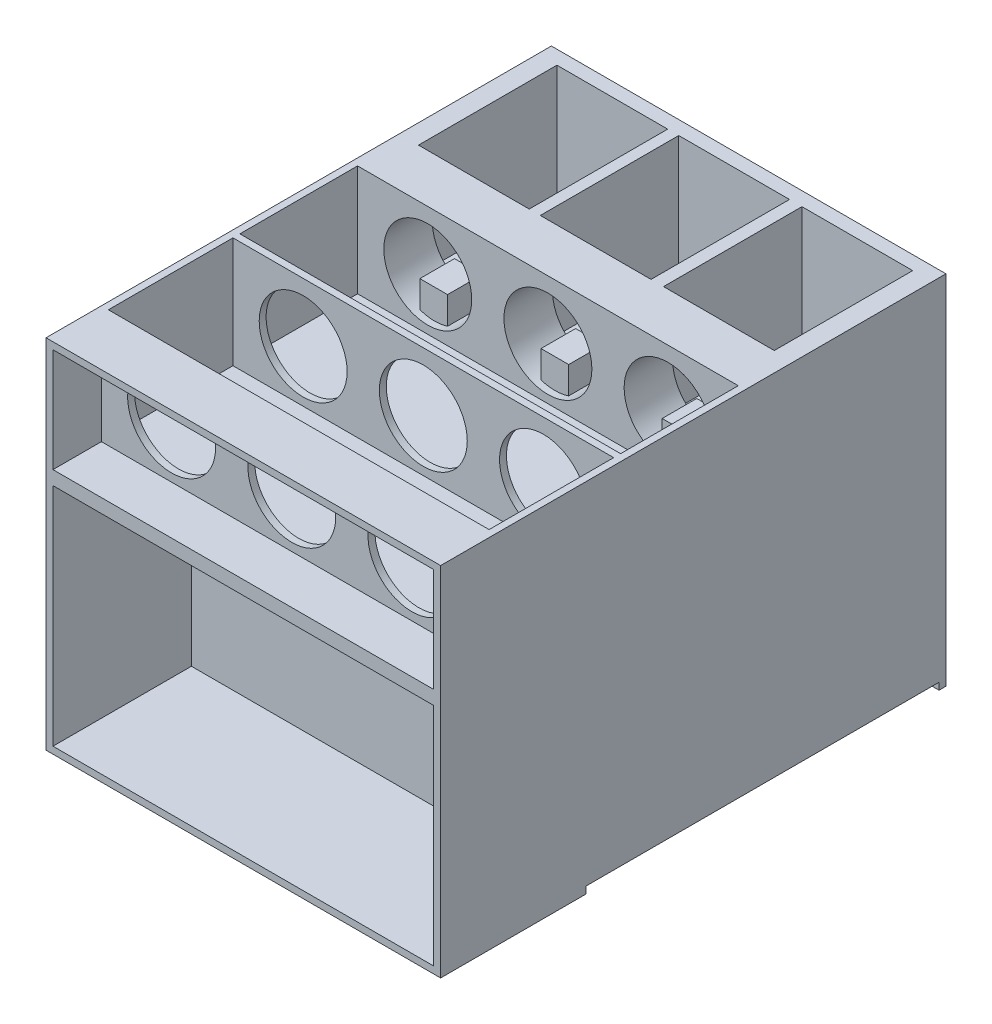
SolidWorks part; units mm, degrees
ref_plane "Front Plane" through (0, 0, 0) normal (0, 0, 1) x (1, 0, 0)
ref_plane "Top Plane" through (0, 0, 0) normal (0, 1, 0) x (1, 0, 0)
ref_plane "Right Plane" through (0, 0, 0) normal (1, 0, 0) x (0, 0, -1)
sketch "Sketch2" plane through (0, 0, 0) normal (0, 0, 1) x (1, 0, 0)
  line L1 (-133.1116, 114.3526) -> (151.8884, 114.3526)
  line L2 (-133.1116, 114.3526) -> (-133.1116, -143.6474)
  line L3 (-133.1116, -143.6474) -> (151.8884, -143.6474)
  line L4 (151.8884, 114.3526) -> (151.8884, -143.6474)
  dimension "D1" = 258
  dimension "D2" = 285
extrude "Boss-Extrude1" add sketch "Sketch2" along normal blind 365
sketch "Sketch3" plane through (0, 0, 365) normal (0, 0, 1) x (1, 0, 0)
  line L0 (151.8884, 114.3526) -> (-133.1116, 114.3526) construction
  line L1 (-128.1116, 109.3526) -> (146.8884, 109.3526)
  line L2 (-128.1116, 109.3526) -> (-128.1116, 34.3526)
  line L3 (-128.1116, 34.3526) -> (146.8884, 34.3526)
  line L4 (146.8884, 109.3526) -> (146.8884, 34.3526)
  line L5 (-133.1116, 114.3526) -> (-133.1116, -143.6474) construction
  line L6 (151.8884, -143.6474) -> (151.8884, 114.3526) construction
  line L7 (-133.1116, -143.6474) -> (151.8884, -143.6474) construction
  line L8 (-128.1116, 24.3526) -> (146.8884, 24.3526)
  line L9 (-128.1116, 24.3526) -> (-128.1116, -138.6474)
  line L10 (-128.1116, -138.6474) -> (146.8884, -138.6474)
  line L11 (146.8884, 24.3526) -> (146.8884, -138.6474)
  dimension "D1" = 5
  dimension "D2" = 5
  dimension "D3" = 5
  dimension "D4" = 75
  dimension "D5" = 10
  dimension "D6" = 5
  dimension "D7" = 5
  dimension "D8" = 5
extrude "Cut-Extrude1" cut sketch "Sketch3" against normal blind 35 contours L2 L1 L4 L3
sketch "Sketch4" plane through (0, 0, 330) normal (0, 0, 1) x (1, 0, 0)
  line L1 (146.8884, 109.3526) -> (146.8884, 34.3526) construction
  line L2 (-128.1116, 109.3526) -> (-128.1116, 34.3526) construction
  line L4 (-128.1116, 109.3526) -> (146.8884, 109.3526) construction
  line L5 (-128.1116, 109.3526) -> (146.8884, 109.3526) construction
  circle A0 centre (-77.4116, 71.8526) radius 31.75
  circle A1 centre (9.3884, 71.8526) radius 31.75
  circle A2 centre (96.1884, 71.8526) radius 31.75
  dimension "D1" = 63.5
  dimension "D2" = 63.5
  dimension "D3" = 63.5
  dimension "D4" = 50.7
  dimension "D5" = 50.7
  dimension "D6" = 137.5
  dimension "D7" = 37.5
  dimension "D8" = 37.5
sketch "Sketch5" plane through (0, 114.3526, 0) normal (0, 1, 0) x (1, 0, 0)
  line L0 (-133.1116, -365) -> (-133.1116, 0) construction
  line L1 (-119.1116, -10) -> (-39.1116, -10)
  line L2 (-119.1116, -10) -> (-119.1116, -110)
  line L3 (-119.1116, -110) -> (-39.1116, -110)
  line L4 (-39.1116, -10) -> (-39.1116, -110)
  line L5 (-31.1116, -10) -> (48.8884, -10)
  line L6 (-31.1116, -10) -> (-31.1116, -110)
  line L7 (-31.1116, -110) -> (48.8884, -110)
  line L8 (48.8884, -10) -> (48.8884, -110)
  line L9 (57.8884, -10) -> (137.8884, -10)
  line L10 (57.8884, -10) -> (57.8884, -110)
  line L11 (57.8884, -110) -> (137.8884, -110)
  line L12 (137.8884, -10) -> (137.8884, -110)
  line L13 (151.8884, 0) -> (-133.1116, 0) construction
  line L14 (151.8884, -365) -> (151.8884, 0) construction
  dimension "D1" = 14
  dimension "D2" = 100
  dimension "D3" = 10
  dimension "D4" = 10
  dimension "D5" = 100
  dimension "D6" = 10
  dimension "D7" = 100
  dimension "D8" = 8
  dimension "8" = 80
  dimension "D9" = 80
  dimension "D10" = 80
  dimension "D11" = 14
  dimension "D12" = 9
  dimension "D13" = 9
  dimension "D14" = 10
extrude "Cut-Extrude2" cut sketch "Sketch5" against normal blind 81 contours L6 L5 L8 L7 | L10 L9 L12 L11 | L2 L1 L4 L3
extrude "Cut-Extrude4" cut sketch "Sketch4" against normal blind 276 contours A0 | A2 | A1
sketch "Sketch6" plane through (0, 114.3526, 0) normal (0, 1, 0) x (1, 0, 0)
  line L0 (151.8884, -365) -> (-133.1116, -365) construction
  line L1 (-128.1116, -145) -> (146.8884, -145)
  line L2 (-128.1116, -145) -> (-128.1116, -230)
  line L3 (-128.1116, -230) -> (146.8884, -230)
  line L4 (146.8884, -145) -> (146.8884, -230)
  line L5 (-128.1116, -235) -> (146.8884, -235)
  line L6 (-128.1116, -235) -> (-128.1116, -325)
  line L7 (-128.1116, -325) -> (146.8884, -325)
  line L8 (146.8884, -235) -> (146.8884, -325)
  line L9 (-133.1116, -365) -> (-133.1116, 0) construction
  line L10 (151.8884, -365) -> (151.8884, 0) construction
  line L11 (-119.1116, -110) -> (-39.1116, -110) construction
  point P14 (-128.1116, -187.5)
  dimension "D1" = 40
  dimension "D2" = 5
  dimension "D3" = 5
  dimension "D4" = 90
  dimension "D5" = 90
  dimension "D6" = 5
  dimension "D7" = 5
  dimension "D8" = 5
  dimension "D9" = 35
extrude "Cut-Extrude6" cut sketch "Sketch6" against normal blind 80
sketch "Sketch8" plane through (0, 0, 365) normal (0, 0, 1) x (1, 0, 0)
  line L0 (-128.1116, 34.3526) -> (146.8884, 34.3526) construction
  line L1 (-128.1116, 24.3526) -> (146.8884, 24.3526)
  line L2 (-128.1116, 24.3526) -> (-128.1116, -138.6474)
  line L3 (-128.1116, -138.6474) -> (146.8884, -138.6474)
  line L4 (146.8884, 24.3526) -> (146.8884, -138.6474)
  line L5 (-133.1116, 114.3526) -> (-133.1116, -143.6474) construction
  line L6 (151.8884, -143.6474) -> (151.8884, 114.3526) construction
  line L7 (-133.1116, -143.6474) -> (151.8884, -143.6474) construction
  dimension "D1" = 10
  dimension "D2" = 5
  dimension "D3" = 5
  dimension "0.5" = 5
extrude "Cut-Extrude10" cut sketch "Sketch8" against normal blind 100
sketch "Sketch16" plane through (0, -143.6474, 0) normal (0, -1, 0) x (1, 0, 0)
  line L1 (-133.1116, 260) -> (151.8884, 260)
  line L2 (-133.1116, 260) -> (-133.1116, 5)
  line L3 (-133.1116, 5) -> (151.8884, 5)
  line L4 (151.8884, 260) -> (151.8884, 5)
  line L5 (-133.1116, 0) -> (151.8884, 0) construction
  line L6 (151.8884, 365) -> (151.8884, 0) construction
  line L7 (-133.1116, 365) -> (-133.1116, 0) construction
  line L8 (-133.1116, 365) -> (151.8884, 365) construction
  dimension "D1" = 5
  dimension "D2" = 0
  dimension "D3" = 0
  dimension "D4" = 105
extrude "Cut-Extrude11" cut sketch "Sketch16" against normal blind 5
sketch "Sketch17" plane through (0, -138.6474, 0) normal (0, -1, 0) x (1, 0, 0)
  line L0 (151.8884, 260) -> (-133.1116, 260) construction
  line L1 (-118.1116, 245) -> (136.8884, 245)
  line L2 (-118.1116, 245) -> (-118.1116, 15)
  line L3 (-118.1116, 15) -> (136.8884, 15)
  line L4 (136.8884, 245) -> (136.8884, 15)
  line L5 (-133.1116, 260) -> (-133.1116, 5) construction
  line L6 (151.8884, 5) -> (151.8884, 260) construction
  line L7 (-133.1116, 5) -> (151.8884, 5) construction
  dimension "D1" = 15
  dimension "D2" = 15
  dimension "D3" = 15
  dimension "D4" = 10
extrude "Cut-Extrude12" cut sketch "Sketch17" against normal blind 165
sketch "Sketch18" plane through (0, 26.3526, 0) normal (0, -1, 0) x (1, 0, 0)
  line L0 (-118.1116, 245) -> (-118.1116, 15) construction
  line L1 (-118.1116, 140) -> (136.8884, 140)
  line L2 (-118.1116, 140) -> (-118.1116, 150)
  line L3 (-118.1116, 150) -> (136.8884, 150)
  line L4 (136.8884, 140) -> (136.8884, 150)
  line L5 (136.8884, 15) -> (136.8884, 245) construction
  line L6 (136.8884, 245) -> (-118.1116, 245) construction
  dimension "D1" = 105
  dimension "D2" = 10
extrude "Boss-Extrude2" add sketch "Sketch18" along normal blind 35
sketch "Sketch19" plane through (0, 26.3526, 0) normal (0, -1, 0) x (1, 0, 0)
  line L0 (-0.6116, 140) -> (19.3884, 140)
  line L2 (-0.6116, 140) -> (-0.6116, 115)
  line L3 (-0.6116, 115) -> (19.3884, 115)
  line L4 (19.3884, 115) -> (19.3884, 140)
  point P7 (9.3884, 140)
  dimension "D1" = 10
  dimension "D2" = 10
  dimension "D3" = 25
extrude "Boss-Extrude3" add sketch "Sketch19" along normal mid plane 70
sketch "Sketch20" plane through (0, 26.3526, 0) normal (0, -1, 0) x (1, 0, 0)
  line L0 (-88.1116, 140) -> (-88.1116, 115)
  line L1 (-118.1116, 140) -> (-0.6116, 140) construction
  line L2 (-88.1116, 115) -> (-68.1116, 115)
  line L3 (-68.1116, 115) -> (-68.1116, 140)
  line L4 (-68.1116, 140) -> (-88.1116, 140)
  line L5 (86.8884, 140) -> (86.8884, 115)
  line L6 (19.3884, 140) -> (136.8884, 140) construction
  line L7 (86.8884, 115) -> (106.8884, 115)
  line L8 (106.8884, 115) -> (106.8884, 140)
  line L10 (-118.1116, 245) -> (-118.1116, 15) construction
  line L11 (86.8884, 140) -> (106.8884, 140)
  line L12 (136.8884, 15) -> (136.8884, 245) construction
  dimension "D1" = 30
  dimension "D2" = 25
  dimension "D3" = 20
  dimension "D4" = 30
  dimension "D5" = 25
  dimension "D6" = 20
extrude "Boss-Extrude4" add sketch "Sketch20" along normal mid plane 70
